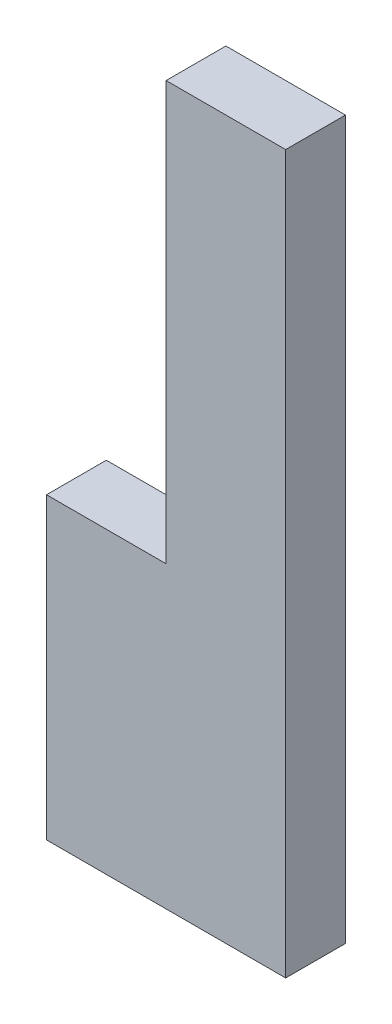
SolidWorks part; units mm, degrees
ref_plane "Plan de face" through (0, 0, 0) normal (0, 0, 1) x (1, 0, 0)
ref_plane "Plan de dessus" through (0, 0, 0) normal (0, 1, 0) x (1, 0, 0)
ref_plane "Plan de droite" through (0, 0, 0) normal (1, 0, 0) x (0, 0, -1)
sketch "Esquisse1" plane through (0, 0, 0) normal (0, 0, 1) x (1, 0, 0)
  line L0 (0, 0) -> (0, 12)
  line L1 (0, 12) -> (-2, 12)
  line L2 (-2, 12) -> (-2, 5)
  line L3 (-2, 5) -> (-4, 5)
  line L4 (-4, 5) -> (-4, 0)
  line L5 (-4, 0) -> (0, 0)
extrude "Extrusion1" add sketch "Esquisse1" along normal blind 1
